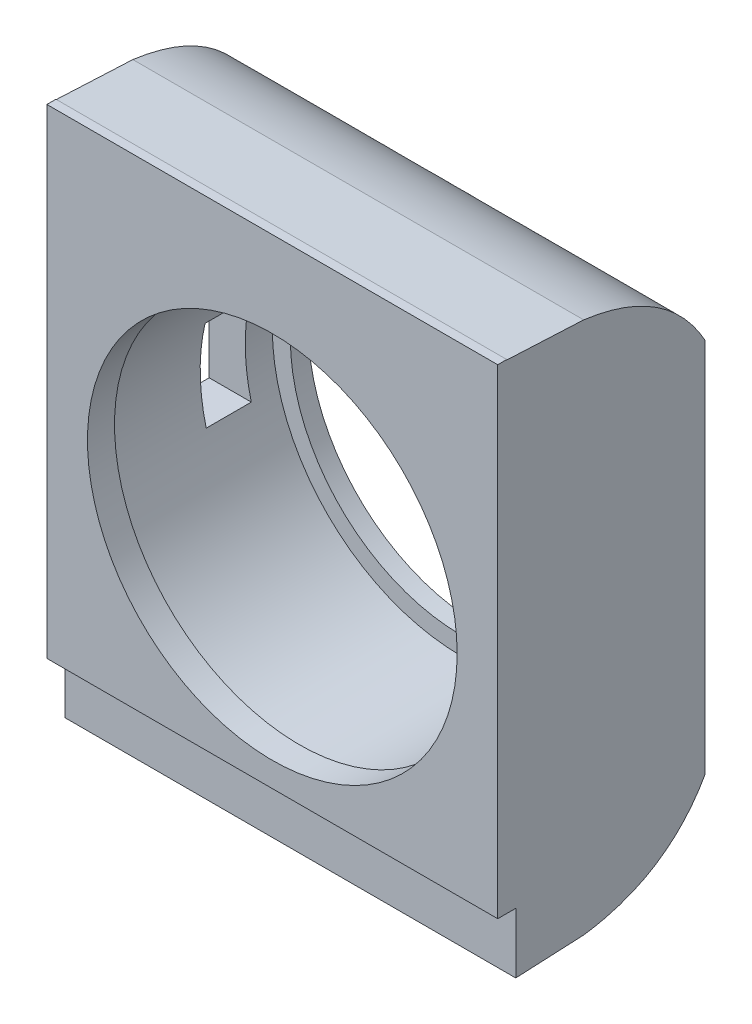
SolidWorks part; units mm, degrees
ref_plane "Front Plane" through (0, 0, 0) normal (0, 0, 1) x (1, 0, 0)
ref_plane "Top Plane" through (0, 0, 0) normal (0, 1, 0) x (1, 0, 0)
ref_plane "Right Plane" through (0, 0, 0) normal (1, 0, 0) x (0, 0, -1)
sketch "Sketch2" plane through (0, 0, 0) normal (0, 0, 1) x (1, 0, 0)
  circle A0 centre (0, 0) radius 21
  circle A1 centre (0, 0) radius 18
  dimension "D1" = 42
  dimension "D2" = 3
extrude "Boss-Extrude1" add sketch "Sketch2" along normal blind 2
sketch "Sketch3" plane through (0, 0, 0) normal (0, 0, 1) x (1, 0, 0)
  circle A2 centre (0, 0) radius 21
  circle A3 centre (0, 0) radius 23
  dimension "D1" = 2
extrude "Boss-Extrude2" add sketch "Sketch3" along normal blind 20 contours A3 | A2
sketch "Sketch5" plane through (0, 0, 0) normal (0, 0, 1) x (1, 0, 0)
  line L1 (-25, 30) -> (25, 30)
  line L2 (-25, 30) -> (-25, -30)
  line L3 (-25, -30) -> (25, -30)
  line L4 (25, 30) -> (25, -30)
  line L5 (-25, 30) -> (25, -30) construction
  line L6 (-25, -30) -> (25, 30) construction
  point P0 (0, 0)
  dimension "D1" = 60
  dimension "D2" = 50
extrude "Boss-Extrude4" add sketch "Sketch5" along normal blind 3 from offset 20
sketch "Sketch6" plane through (0, 0, 0) normal (0, 0, 1) x (1, 0, 0)
  circle A0 centre (0, 0) radius 22
  dimension "D1" = 44
extrude "Cut-Extrude5" cut sketch "Sketch6" along normal blind 5 from offset 20
sketch "Sketch7" plane through (0, 0, 0) normal (0, 0, 1) x (1, 0, 0)
  circle A0 centre (0, 0) radius 20.5
  circle A1 centre (0, 0) radius 22
  dimension "D1" = 41
extrude "Boss-Extrude5" add sketch "Sketch7" along normal blind 3 from offset 20
sketch "Sketch11" plane through (0, 0, 0) normal (0, 0, 1) x (1, 0, 0)
  line L1 (25, 30) -> (-25, 30)
  line L2 (25, 30) -> (25, -30)
  line L3 (25, -30) -> (-25, -30)
  line L4 (-25, 30) -> (-25, -30)
  line L5 (25, 30) -> (-25, -30) construction
  line L6 (25, -30) -> (-25, 30) construction
  circle A0 centre (0, 0) radius 23
  point P0 (0, 0)
extrude "Boss-Extrude13" add sketch "Sketch11" along normal blind 20
sketch "Sketch13" plane through (0, 0, 0) normal (1, 0, 0) x (0, 0, -1)
  line L0 (57.3947, 0) -> (-57.3947, 0) construction
  line L7 (0, 30) -> (0, -30) construction
  line L8 (-13.4694, 29.5428) -> (-23, 30)
  line L9 (-23, 30) -> (-23, -30) construction
  line L10 (-23, 30) -> (0, 30) construction
  line L11 (0, 20.8432) -> (0, 33.8929)
  line L12 (0, 33.8929) -> (-23, 33.8929)
  line L13 (-23, 33.8929) -> (-23, 30)
  line L14 (-23, -33.8929) -> (-23, -30)
  line L15 (0, -33.8929) -> (-23, -33.8929)
  line L16 (0, -20.8432) -> (0, -33.8929)
  line L17 (-13.4694, -29.5428) -> (-23, -30)
  spline S0 degree 2 poles (0, 20.8432) (-4.171, 28.2897) (-13.4694, 29.5428) knots 0 0 0 1 1 1
  spline S1 degree 2 poles (0, -20.8432) (-4.171, -28.2897) (-13.4694, -29.5428) knots 0 0 0 1 1 1
  point P3 (0, 0)
  point P6 (-13.4694, 29.5428)
extrude "Cut-Extrude8" cut sketch "Sketch13" against normal through all both and the other way through all
sketch "Sketch14" plane through (0, 0, 0) normal (1, 0, 0) x (0, 0, -1)
  line L0 (0, 20.8432) -> (0, -20.8432) construction
  line L1 (-10, 4.7425) -> (-5, 4.7425)
  line L2 (-10, 4.7425) -> (-10, -5.2575)
  line L3 (-10, -5.2575) -> (-5, -5.2575)
  line L4 (-5, 4.7425) -> (-5, -5.2575)
  line L5 (-10, 4.7425) -> (-5, -5.2575) construction
  line L6 (-10, -5.2575) -> (-5, 4.7425) construction
  point P0 (-7.5, -0.2575)
  point P5 (-8.2842, -0.2575)
  dimension "D1" = 5
  dimension "D2" = 10
  dimension "D3" = 5
extrude "Cut-Extrude9" cut sketch "Sketch14" against normal blind 30
sketch "Sketch16" plane through (0, 0, 0) normal (0, 0, 1) x (1, 0, 0)
  line L0 (25, -30) -> (25, 30) construction
  line L1 (-25, 30) -> (25, 30)
  line L2 (-25, 30) -> (-25, -23.9)
  line L3 (-25, -23.9) -> (25, -23.9)
  line L4 (25, 30) -> (25, -23.9)
  circle A0 centre (0, 0) radius 21
  dimension "D1" = 53.9
extrude "Boss-Extrude14" add sketch "Sketch16" along normal blind 5 from offset 22 contours A0 L3 L4 L1 L2
sketch "Sketch17" plane through (0, 0, 0) normal (1, 0, 0) x (0, 0, -1)
  line L0 (0, 20.8432) -> (0, -20.8432) construction
  line L1 (0, 0) -> (-23, 0)
  line L2 (0, 0) -> (0, -32.2957)
  line L3 (0, -32.2957) -> (-23, -32.2957)
  line L4 (-23, 0) -> (-23, -32.2957)
  line L6 (-27, -23.9) -> (-23, -23.9)
  line L7 (-27, -23.9) -> (-27, 35.5974)
  line L8 (-27, 35.5974) -> (-23, 35.5974)
  line L9 (-23, -23.9) -> (-23, 35.5974)
  dimension "D1" = 23
extrude "Cut-Extrude10" cut sketch "Sketch17" against normal through all both and the other way through all contours L4 L9 L8 L7 L6
sketch "Sketch18" plane through (0, 0, 0) normal (1, 0, 0) x (0, 0, -1)
  line L1 (-23, -30) -> (-21, -30)
  line L2 (-23, -30) -> (-23, -23.2103)
  line L3 (-23, -23.2103) -> (-21, -23.2103)
  line L4 (-21, -30) -> (-21, -23.2103)
  line L5 (-23, -23.2103) -> (-21, -23.2103)
  line L6 (-23, -23.2103) -> (-23, 29.7897)
  line L7 (-23, 29.7897) -> (-21, 29.7897)
  line L8 (-21, -23.2103) -> (-21, 29.7897)
  dimension "D1" = 53
  dimension "D2" = 2
extrude "Cut-Extrude11" cut sketch "Sketch18" against normal through all both and the other way through all contours L1 L4 L3 L2
sketch "Sketch19" plane through (0, 0, 0) normal (0, 0, 1) x (1, 0, 0)
  circle A0 centre (0, 0) radius 21
  circle A1 centre (0, 0) radius 19
  circle A2 centre (0, 0) radius 18
  dimension "D1" = 1
extrude "Cut-Extrude13" cut sketch "Sketch19" against normal through all and the other way through all contours A1 A2
